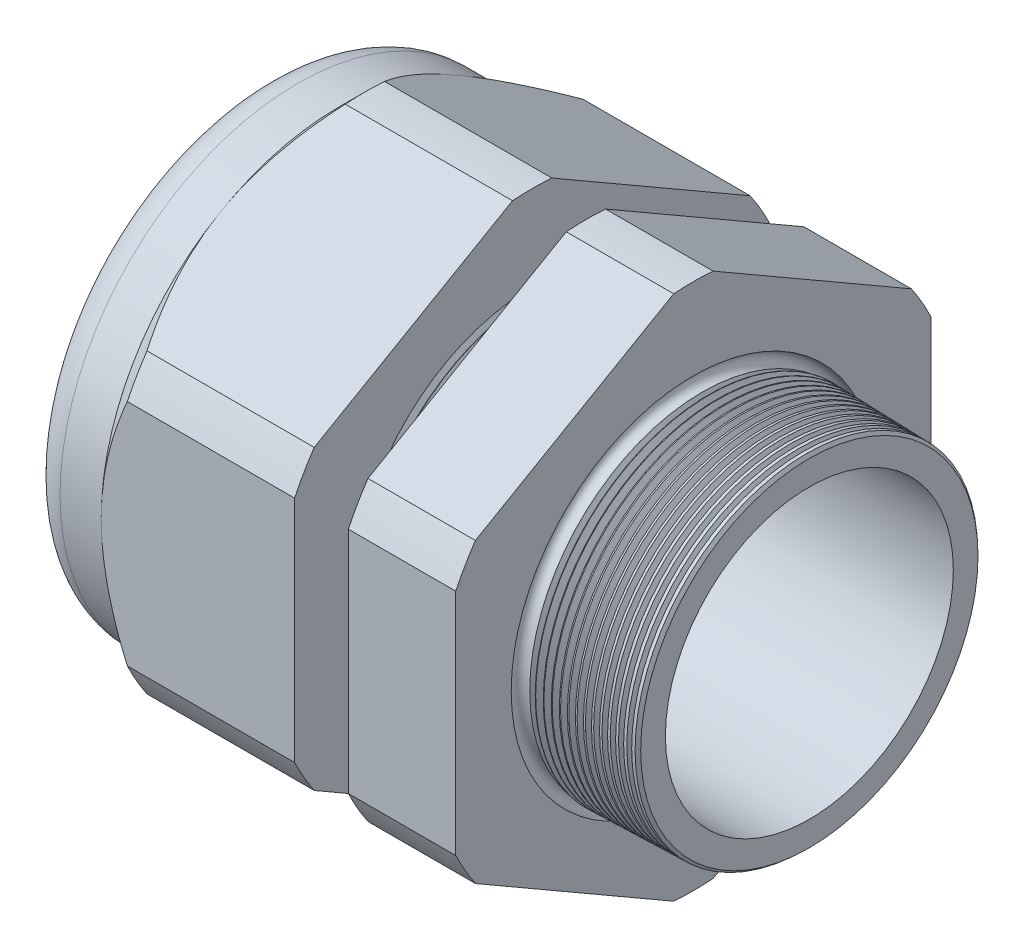
SolidWorks part; units mm, degrees
ref_plane "Front Plane" through (0, 0, 0) normal (0, 0, 1) x (1, 0, 0)
ref_plane "Top Plane" through (0, 0, 0) normal (0, 1, 0) x (1, 0, 0)
ref_plane "Right Plane" through (0, 0, 0) normal (1, 0, 0) x (0, 0, -1)
sketch "Sketch10" plane through (0, 0, 0) normal (0, 0, 1) x (1, 0, 0)
  line L0 (0, 0) -> (-115.3565, 0) construction
  line L1 (-55.88, 16.002) -> (-25.8776, 16.002)
  line L2 (5.08, 16.0803) -> (5.08, 19.1283)
  line L3 (-7.874, 19.4676) -> (5.08, 19.1283)
  line L4 (-7.874, 53.086) -> (-7.874, 19.4676)
  line L5 (-7.874, 53.086) -> (-19.874, 53.086)
  line L6 (-19.874, 53.086) -> (-19.874, 19.7818)
  line L7 (-25.8776, 19.939) -> (-19.874, 19.7818)
  line L8 (-25.8776, 19.939) -> (-25.8776, 53.086)
  line L9 (-25.8776, 53.086) -> (-47.48, 53.086)
  line L10 (-47.48, 53.086) -> (-47.48, 26.543)
  line L11 (-47.48, 26.543) -> (-55.88, 26.543)
  line L12 (-55.88, 26.543) -> (-55.88, 16.002)
  line L13 (-25.8776, 16.002) -> (5.08, 16.0803)
  dimension "D1" = 60.96
  dimension "D2" = 32.004
  dimension "D3" = 1.5
  dimension "D4" = 3.048
  dimension "A" = 39.878
  dimension "D6" = 53.086
  dimension "D8" = 106.172
  dimension "D9" = 8.4
  dimension "D10" = 21.6024
  dimension "D11" = 12
  dimension "D" = 12.954
revolve "Revolve2" add sketch "Sketch10" angle 360 about L0
sketch "Sketch12" plane through (-47.48, 0, 0) normal (-1, 0, 0) x (0, 0, 1)
  line L1 (-2.1972, 29.3807) -> (-24.3458, 16.5931)
  line L2 (-26.543, 12.7876) -> (-26.543, -12.7876)
  line L3 (-24.3458, -16.5931) -> (-2.1972, -29.3807)
  line L4 (2.1972, -29.3807) -> (24.3458, -16.5931)
  line L5 (26.543, -12.7876) -> (26.543, 12.7876)
  line L6 (24.3458, 16.5931) -> (2.1972, 29.3807)
  circle A0 centre (0, 0) radius 26.543 construction
  arc A1 (2.1972, 29.3807) -> (-2.1972, 29.3807) centre (0, 0) ccw
  arc A2 (-24.3458, 16.5931) -> (-26.543, 12.7876) centre (0, 0) ccw
  arc A3 (-26.543, -12.7876) -> (-24.3458, -16.5931) centre (0, 0) ccw
  arc A4 (-2.1972, -29.3807) -> (2.1972, -29.3807) centre (0, 0) ccw
  arc A5 (24.3458, -16.5931) -> (26.543, -12.7876) centre (0, 0) ccw
  arc A6 (26.543, 12.7876) -> (24.3458, 16.5931) centre (0, 0) ccw
  dimension "D2" = 58.9255
  dimension "D1" = 53.086
extrude "Cut-Extrude2" cut sketch "Sketch12" against normal through all flip side to cut
fillet "Fillet4" radius 3.81 1 edges at (-55.88, 0, -26.543)
sketch "Sketch19" plane through (-47.48, 0, 0) normal (-1, 0, 0) x (0, 0, 1)
  line L0 (26.543, 0) -> (26.543, 12.7876) construction
  circle A0 centre (0, 0) radius 26.543
extrude "Cut-Extrude3" cut sketch "Sketch19" against normal blind 3.998 draft 45 flip side to cut
chamfer "Chamfer1" distance 0.254 angle 45 1 edges at (5.08, 0, -19.1283)
sketch "Sketch21" plane through (-55.88, 0, 0) normal (-1, 0, 0) x (0, 0, 1)
  circle A0 centre (0, 0) radius 16.002
  circle A2 centre (0, 0) radius 16.002 construction
extrude "plug" add sketch "Sketch21" against normal blind 12.7 separate body
sketch "Sketch22" plane through (-55.88, 0, 0) normal (-1, 0, 0) x (0, 0, 1)
  circle A0 centre (0, 0) radius 15.748
  circle A1 centre (0, 0) radius 16.002 construction
  dimension "D1" = 0.254
extrude "Cut-Extrude4" cut sketch "Sketch22" against normal blind 0.508
sketch "Sketch27" plane through (-55.372, 0, 0) normal (-1, 0, 0) x (0, 0, 1)
  line L0 (-4.3624, 0) -> (4.3624, 0) construction
  circle A0 centre (-11.2852, 0) radius 4.445
  circle A1 centre (0, 0) radius 15.748 construction
  dimension "D1" = 0.0178
  dimension "holedia" = 8.89
extrude "plugholes" cut sketch "Sketch27" against normal through all
pattern_circular "CirPattern1" count 5 over 360 about axis through (0, 0, 0) along (1, 0, 0) of "plugholes"
sketch "Sketch28" [suppressed] plane through (-38.354, 0, 0) normal (-1, 0, 0) x (0, 0, 1)
  circle A0 centre (0, 0) radius 1.905
  dimension "midholedia" = 8.89
extrude "midhole" [suppressed] cut sketch "Sketch28" against normal through all
sketch "Sketch29" plane through (0, 0, 0) normal (0, 0, 1) x (1, 0, 0)
  line L0 (-25.8776, 19.939) -> (-25.1446, 19.9198)
  line L1 (-19.874, 19.7818) -> (-25.8776, 19.939) construction
  line L2 (-25.1446, 19.9198) -> (-25.5277, 19.2946)
  line L3 (-25.5277, 19.2946) -> (-25.8776, 19.939)
  dimension "D1" = 60
  dimension "D2" = 60
  dimension "D3" = 0.635
revolve "Cut-Revolve1" cut sketch "Sketch29" angle 360 about axis through (0, 0, 0) along (-1, 0, 0)
pattern_linear "LPattern1" count 8 spacing 0.762 along (1, 0, 0) of "Cut-Revolve1"
sketch "Sketch30" plane through (0, 0, 0) normal (0, 0, 1) x (1, 0, 0)
  line L0 (-7.874, 19.4676) -> (-6.9944, 19.4445)
  line L1 (-7.874, 29.3807) -> (-7.874, 16.5931) construction
  line L2 (4.8261, 19.135) -> (-7.874, 19.4676) construction
  line L3 (-6.9944, 19.4445) -> (-7.4542, 18.6943)
  line L4 (-7.4542, 18.6943) -> (-7.874, 19.4676)
  dimension "D1" = 60
  dimension "D2" = 60
  dimension "D3" = 0.762
revolve "Cut-Revolve2" cut sketch "Sketch30" angle 360 about axis through (0, 0, 0) along (-1, 0, 0)
pattern_linear "LPattern2" count 15 spacing 0.889 along (1, 0, 0) of "Cut-Revolve2"
sketch "Sketch31" [suppressed] plane through (-38.354, 0, 0) normal (-1, 0, 0) x (0, 0, 1)
  line L0 (-1.905, 1.905) -> (1.905, 1.905)
  line L1 (-1.905, -1.905) -> (1.905, -1.905)
  circle A0 centre (0, 0) radius 1.905 construction
  arc A1 (-1.905, 1.905) -> (-1.905, -1.905) centre (-1.905, 0) ccw
  arc A2 (1.905, 1.905) -> (1.905, -1.905) centre (1.905, 0) cw
extrude "Cut-Extrude5" [suppressed] cut sketch "Sketch31" against normal through all
sketch "Sketch32" plane through (0, 0, 0) normal (0, 0, 1) x (1, 0, 0)
  line L0 (-7.874, 29.3807) -> (-7.874, 16.5931) construction
  circle A0 centre (-7.747, 19.4676) radius 0.889
  dimension "D2" = 1.778
  dimension "D1" = 0.127
revolve "Cut-Revolve3" cut sketch "Sketch32" angle 360 about axis through (0, 0, 0) along (-1, 0, 0)
